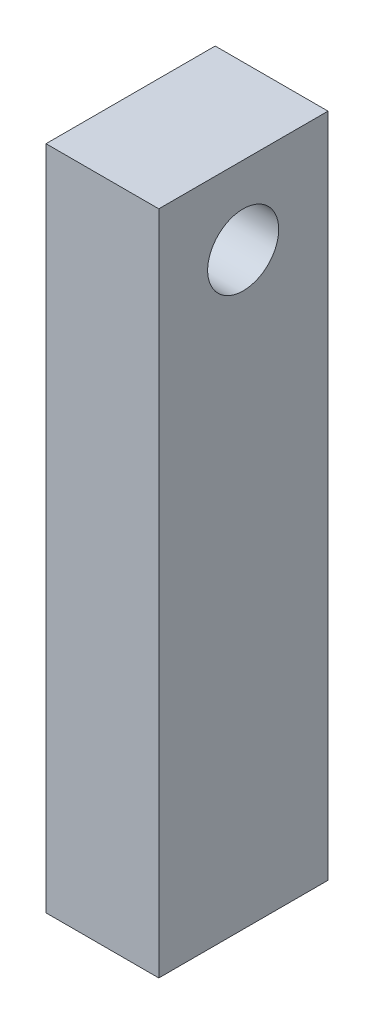
SolidWorks part; units mm, degrees
ref_plane "Front Plane" through (0, 0, 0) normal (0, 0, 1) x (1, 0, 0)
ref_plane "Top Plane" through (0, 0, 0) normal (0, 1, 0) x (1, 0, 0)
ref_plane "Right Plane" through (0, 0, 0) normal (1, 0, 0) x (0, 0, -1)
sketch "Sketch1" plane through (0, 0, 0) normal (0, 1, 0) x (1, 0, 0)
  line L1 (0, 0) -> (50.8, 0)
  line L2 (0, 0) -> (0, 76.2)
  line L3 (0, 76.2) -> (50.8, 76.2)
  line L4 (50.8, 0) -> (50.8, 76.2)
  dimension "D1" = 50.8
  dimension "D2" = 76.2
extrude "Boss-Extrude1" add sketch "Sketch1" along normal blind 300
sketch "Sketch2" plane through (50.8, 0, 0) normal (1, 0, 0) x (0, 0, -1)
  line L1 (0, 0) -> (38, 0)
  line L2 (0, 0) -> (0, 265)
  line L3 (0, 265) -> (38, 265)
  line L4 (38, 0) -> (38, 265)
  circle A0 centre (38, 265) radius 16
  dimension "D1" = 38
  dimension "D2" = 265
extrude "Cut-Extrude1" cut sketch "Sketch2" against normal blind 150 contours L4 A0 L3 | L3 A0 L4
